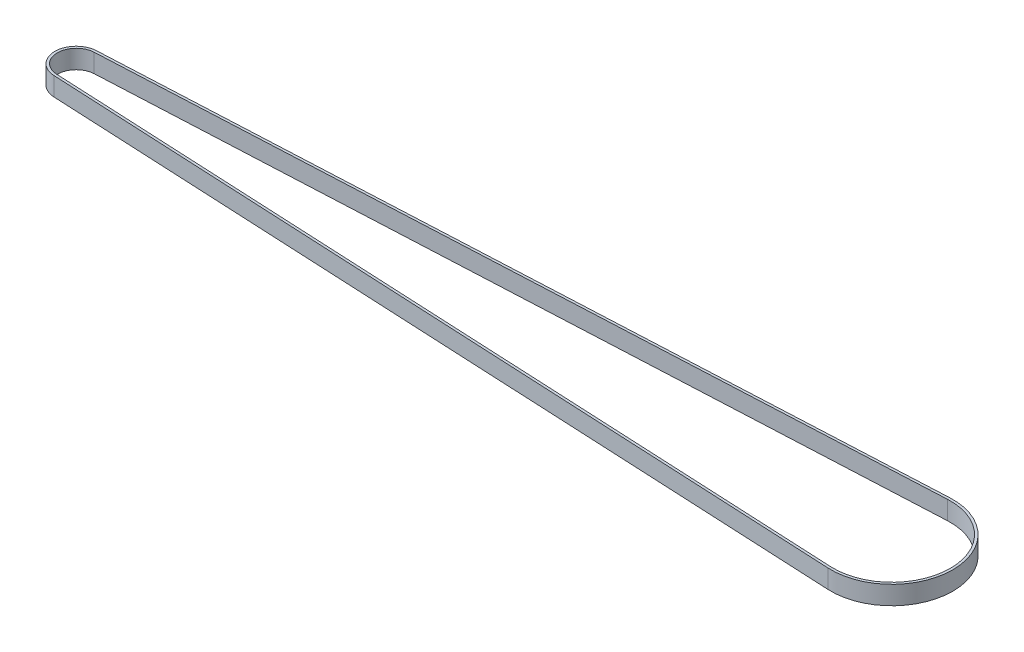
SolidWorks part; units mm, degrees
material "NEOPRENE"
ref_plane "Front Plane" through (0, 0, 0) normal (0, 0, 1) x (1, 0, 0)
ref_plane "Top Plane" through (0, 0, 0) normal (0, 1, 0) x (1, 0, 0)
ref_plane "Right Plane" through (0, 0, 0) normal (1, 0, 0) x (0, 0, -1)
sketch "Sketch1" plane through (0, 0, 0) normal (0, 1, 0) x (1, 0, 0)
  line L0 (-0.2957, 6.0928) -> (262.0862, 18.8278)
  line L1 (-0.2957, -6.0928) -> (262.0862, -18.8278)
  line L2 (0, 0) -> (263, 0) construction
  line L3 (-0.3345, -6.8919) -> (262.0474, -19.6269)
  line L4 (-0.3345, 6.8919) -> (262.0474, 19.6269)
  arc A0 (-0.2957, 6.0928) -> (-0.2957, -6.0928) centre (0, 0) ccw
  arc A1 (262.0862, 18.8278) -> (262.0862, -18.8278) centre (263, 0) cw
  arc A2 (262.0474, 19.6269) -> (262.0474, -19.6269) centre (263, 0) cw
  arc A3 (-0.3345, 6.8919) -> (-0.3345, -6.8919) centre (0, 0) ccw
  dimension "D1" = 6.1
  dimension "D2" = 18.85
  dimension "D3" = 263
  dimension "D4" = 0.8
extrude "Boss-Extrude1" add sketch "Sketch1" along normal blind 6
